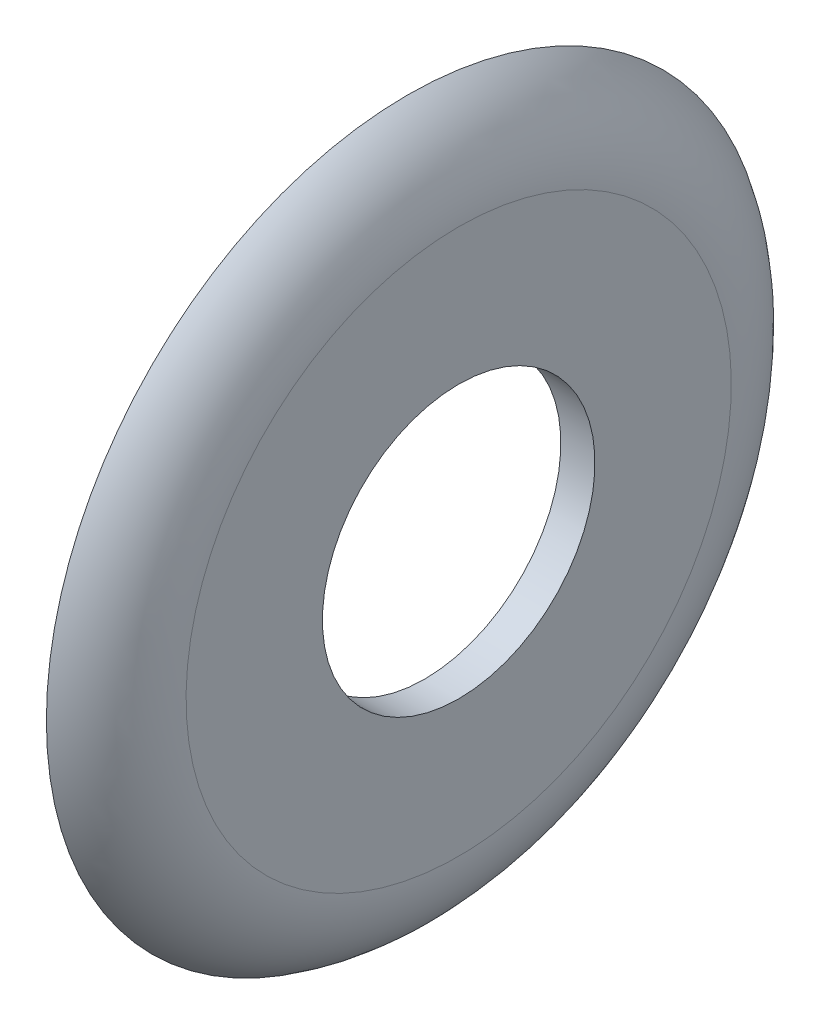
SolidWorks part; units mm, degrees
ref_plane "Front Plane" through (0, 0, 0) normal (0, 0, 1) x (1, 0, 0)
ref_plane "Top Plane" through (0, 0, 0) normal (0, 1, 0) x (1, 0, 0)
ref_plane "Right Plane" through (0, 0, 0) normal (1, 0, 0) x (0, 0, -1)
sketch "Sketch2" plane through (0, 0, 0) normal (0, 0, 1) x (1, 0, 0)
  line L0 (6.4796, 0) -> (-6.4796, 0)
  line L1 (6.4796, 7.9951) -> (6.4796, 15.9951)
  line L2 (6.4796, 7.9951) -> (4.4796, 7.9951)
  line L3 (4.4796, 7.9951) -> (4.4796, 15.9951)
  line L4 (4.4796, 7.9951) -> (3.4796, 7.9951)
  line L6 (3.4796, 7.9951) -> (3.4796, 21.1913)
  arc A0 (3.4796, 21.1913) -> (6.4796, 15.9951) centre (0.4796, 15.9951) cw
  arc A1 (3.4796, 19.3117) -> (4.4796, 15.9951) centre (-1.5204, 15.9951) cw
  point P4 (0, 0)
  dimension "D1" = 6
  dimension "D2" = 6
  dimension "D3" = 2
  dimension "D4" = 1
revolve "Revolve1" add sketch "Sketch2" angle 360 about L0
